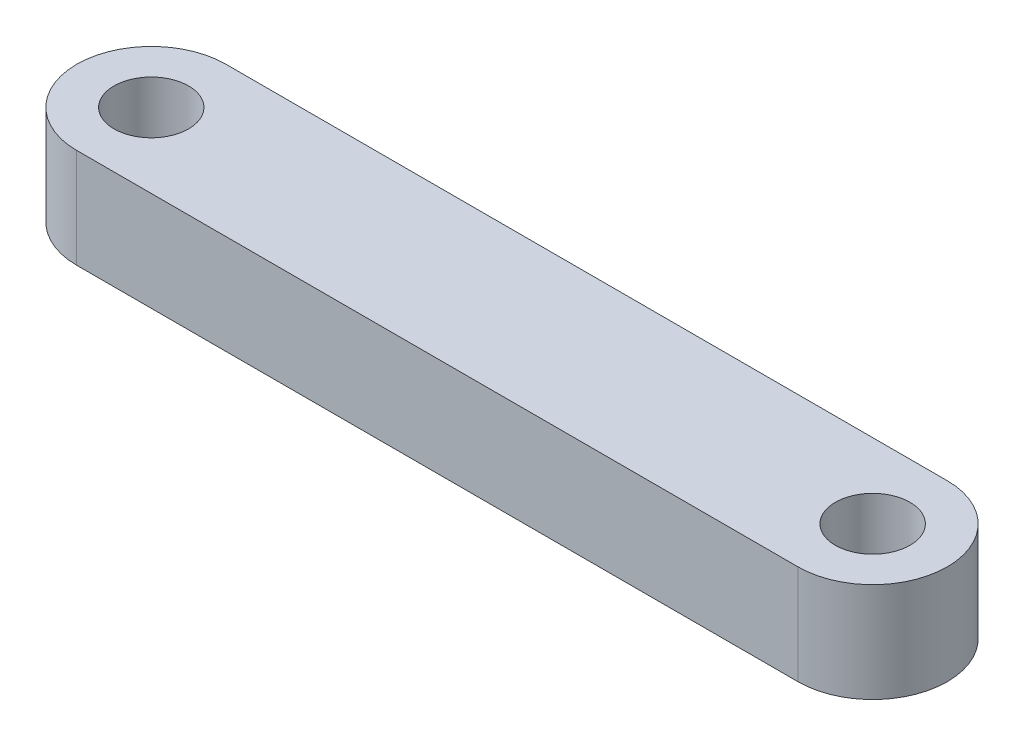
SolidWorks part; units mm, degrees
ref_plane "Alzado" through (0, 0, 0) normal (0, 0, 1) x (1, 0, 0)
ref_plane "Planta" through (0, 0, 0) normal (0, 1, 0) x (1, 0, 0)
ref_plane "Vista lateral" through (0, 0, 0) normal (1, 0, 0) x (0, 0, -1)
sketch "Croquis1" plane through (0, 0, 0) normal (0, 1, 0) x (1, 0, 0)
  line L0 (-14.9955, 4.3625) -> (14.0045, 4.3625)
  line L1 (14.0045, -1.6375) -> (-14.9955, -1.6375)
  arc A0 (-14.9955, 4.3625) -> (-14.9955, -1.6375) centre (-14.9955, 1.3625) ccw
  arc A1 (14.0045, -1.6375) -> (14.0045, 4.3625) centre (14.0045, 1.3625) ccw
  circle A2 centre (14.0045, 1.3625) radius 1.5
  circle A3 centre (-14.9937, 1.359) radius 1.4985
extrude "Saliente-Extruir1" add sketch "Croquis1" along normal blind 4
